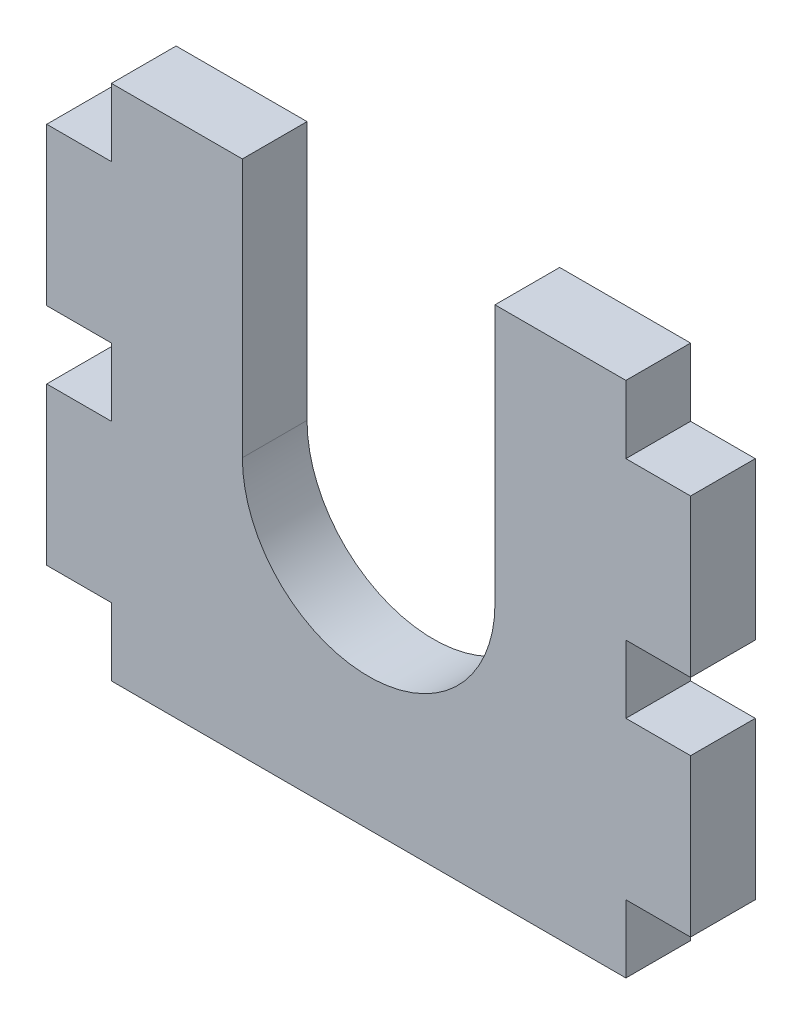
SolidWorks part; units mm, degrees
other "Markup1"
sketch "Sketch8" plane through (0, 42.672, 7.62) normal (-0.0219, 0.0577, 0.9981) x (0.9973, -0.0687, 0.0258)
ref_plane "Front Plane" through (0, 0, 0) normal (0, 0, 1) x (1, 0, 0)
ref_plane "Top Plane" through (0, 0, 0) normal (0, 1, 0) x (1, 0, 0)
ref_plane "Right Plane" through (0, 0, 0) normal (1, 0, 0) x (0, 0, -1)
sketch "Sketch1" plane through (0, 0, 0) normal (0, 0, 1) x (1, 0, 0)
  line L1 (0, 0) -> (53.086, 0)
  line L2 (0, 0) -> (0, 42.672)
  line L3 (0, 42.672) -> (53.086, 42.672)
  line L4 (53.086, 0) -> (53.086, 42.672)
  dimension "D1" = 53.086
  dimension "D2" = 42.672
extrude "Boss-Extrude1" add sketch "Sketch1" along normal blind 5.334
sketch "Sketch2" plane through (0, 0, 5.334) normal (0, 0, 1) x (1, 0, 0)
  line L1 (0, 42.672) -> (5.334, 42.672)
  line L2 (0, 42.672) -> (0, 37.084)
  line L3 (0, 37.084) -> (5.334, 37.084)
  line L4 (5.334, 42.672) -> (5.334, 37.084)
  dimension "D1" = 5.588
  dimension "D2" = 5.334
extrude "Cut-Extrude1" cut sketch "Sketch2" against normal through all contours L2 L1 L4 L3
sketch "Sketch3" plane through (0, 0, 5.334) normal (0, 0, 1) x (1, 0, 0)
  line L0 (0, 37.084) -> (0, 0) construction
  line L1 (0, 24.13) -> (5.334, 24.13)
  line L2 (0, 24.13) -> (0, 18.542)
  line L3 (0, 18.542) -> (5.334, 18.542)
  line L4 (5.334, 24.13) -> (5.334, 18.542)
  line L5 (0, 37.084) -> (5.334, 37.084) construction
  dimension "D2" = 5.334
  dimension "D1" = 12.954
  dimension "D3" = 5.588
extrude "Cut-Extrude2" cut sketch "Sketch3" against normal through all contours L2 L1 L4 L3
sketch "Sketch4" plane through (0, 0, 5.334) normal (0, 0, 1) x (1, 0, 0)
  line L1 (0, 0) -> (5.334, 0)
  line L2 (0, 0) -> (0, 5.588)
  line L3 (0, 5.588) -> (5.334, 5.588)
  line L4 (5.334, 0) -> (5.334, 5.588)
  dimension "D1" = 5.334
  dimension "corner" = 5.588
extrude "Cut-Extrude3" cut sketch "Sketch4" against normal through all
sketch "Sketch5" plane through (0, 0, 5.334) normal (0, 0, 1) x (1, 0, 0)
  line L1 (53.086, 42.672) -> (47.752, 42.672)
  line L2 (53.086, 42.672) -> (53.086, 37.084)
  line L3 (53.086, 37.084) -> (47.752, 37.084)
  line L4 (47.752, 42.672) -> (47.752, 37.084)
  dimension "D1" = 5.588
  dimension "D2" = 5.334
extrude "Cut-Extrude4" cut sketch "Sketch5" against normal through all
sketch "Sketch6" plane through (0, 0, 5.334) normal (0, 0, 1) x (1, 0, 0)
  line L0 (53.086, 0) -> (53.086, 37.084) construction
  line L1 (53.086, 18.542) -> (47.752, 18.542)
  line L2 (53.086, 18.542) -> (53.086, 24.13)
  line L3 (53.086, 24.13) -> (47.752, 24.13)
  line L4 (47.752, 18.542) -> (47.752, 24.13)
  line L6 (53.086, 0) -> (47.752, 0)
  line L7 (53.086, 0) -> (53.086, 5.588)
  line L8 (53.086, 5.588) -> (47.752, 5.588)
  line L9 (47.752, 0) -> (47.752, 5.588)
  dimension "D1" = 5.334
  dimension "D2" = 5.334
  dimension "D3" = 5.588
  dimension "D4" = 5.588
extrude "Cut-Extrude5" cut sketch "Sketch6" against normal through all contours L2 L1 L4 L3 | L7 L6 L9 L8
sketch "Sketch10" plane through (0, 0, 5.334) normal (0, 0, 1) x (1, 0, 0)
  line L0 (5.334, 21.336) -> (47.752, 21.336) construction
  line L1 (5.334, 18.542) -> (5.334, 24.13) construction
  line L2 (47.752, 18.542) -> (47.752, 24.13) construction
sketch "Sketch11" plane through (0, 0, 5.334) normal (0, 0, 1) x (1, 0, 0)
  line L0 (26.543, 42.672) -> (26.543, 0) construction
  line L1 (47.752, 42.672) -> (5.334, 42.672) construction
  line L2 (5.334, 0) -> (47.752, 0) construction
  line L3 (16.129, 21.336) -> (16.129, 42.672)
  line L4 (36.957, 21.336) -> (36.957, 42.672)
  line L5 (36.957, 42.672) -> (16.129, 42.672)
  arc A1 (16.129, 21.336) -> (36.957, 21.336) centre (26.543, 21.336) ccw
extrude "Cut-Extrude6" cut sketch "Sketch11" against normal through all
equation "\"D1@Boss-Extrude1\"=\"GMaterial\""
equation "\"GMaterial\" = 0.21in"
equation "\"Foamcore\"= 0.2in"
equation "\"MDF\"= 0.21in"
equation "\"D2@Sketch2\"=\"GMaterial\""
equation "\"D2@Sketch3\"=\"GMaterial\""
equation "\"D1@Sketch4\"=\"GMaterial\""
equation "\"D2@Sketch5\"=\"GMaterial\""
equation "\"D1@Sketch6\"=\"GMaterial\""
equation "\"D2@Sketch6\"=\"GMaterial\""
equation "\"D3@Sketch6\"=0.22"
equation "\"backside\"= 1.67 + ( 2 * \"GMaterial\" )"
equation "\"D1@Sketch1\"=\"backside\""
